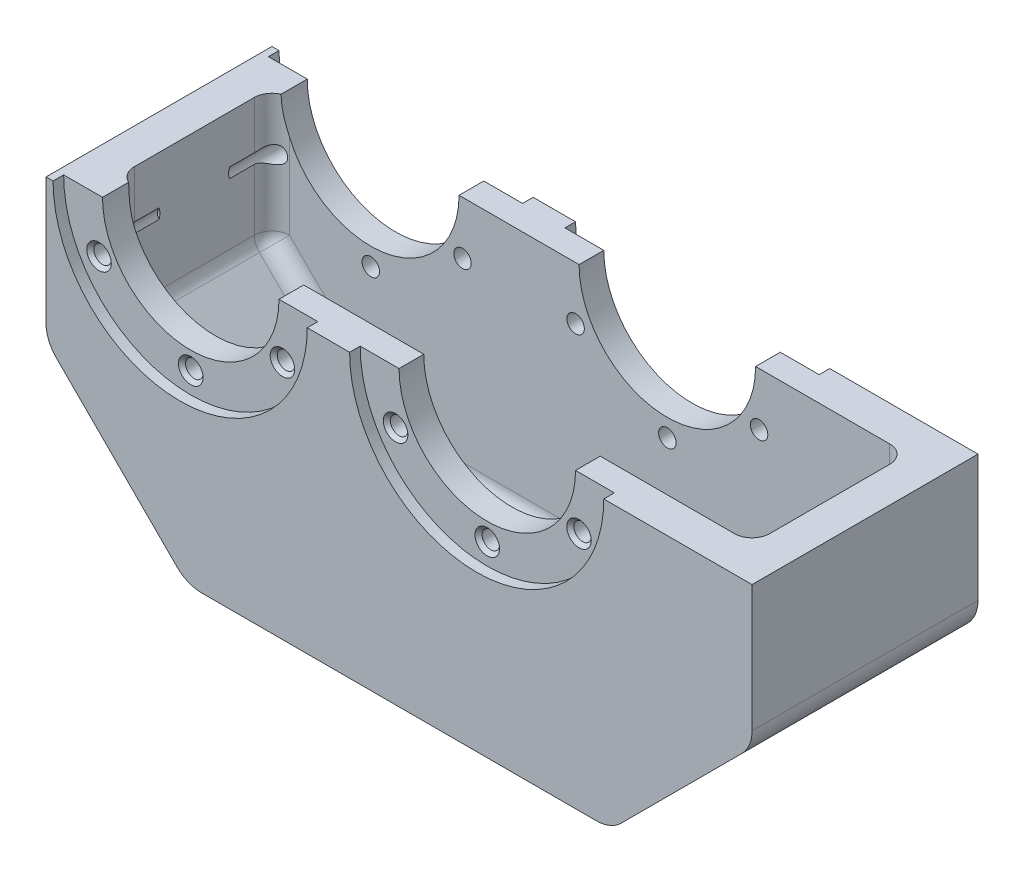
SolidWorks part; units mm, degrees
material "Сталь 20 ГОСТ 1050-88"
ref_plane "Plane1" through (0, 0, 0) normal (0, 0, 1) x (1, 0, 0)
ref_plane "Plane2" through (0, 0, 0) normal (0, 1, 0) x (1, 0, 0)
ref_plane "Plane3" through (0, 0, 0) normal (1, 0, 0) x (0, 0, -1)
sketch "Эскиз1" plane through (0, 0, 0) normal (0, 0, 1) x (1, 0, 0)
  line L0 (-38, 0) -> (-25, 0)
  line L1 (-38, 0) -> (-38, -40)
  line L2 (2, -80) -> (122, -80)
  line L3 (162, -40) -> (162, 0)
  line L4 (25, 0) -> (59, 0)
  line L5 (-38, -40) -> (2, -80)
  line L6 (162, -40) -> (122, -80)
  line L7 (109, 0) -> (162, 0)
  arc A0 (-25, 0) -> (25, 0) centre (0, 0) ccw
  arc A1 (59, 0) -> (109, 0) centre (84, 0) ccw
  dimension "D1" = 50
  dimension "D8" = 84
  dimension "D2" = 38
  dimension "D3" = 80
  dimension "D4" = 200
  dimension "D5" = 45
  dimension "D6" = 45
  dimension "D7" = 40
extrude "Бобышка-Вытянуть1" add sketch "Эскиз1" along normal mid plane 64
shell "Оболочка1" thickness 10
sketch "Эскиз2" plane through (0, 0, 32) normal (0, 0, 1) x (1, 0, 0)
  circle A0 centre (0, 0) radius 36
  circle A1 centre (84, 0) radius 36
  dimension "D1" = 72
extrude "Вырез-Вытянуть1" cut sketch "Эскиз2" against normal blind 3
sketch "Эскиз3" plane through (0, 0, -32) normal (0, 0, -1) x (-1, 0, 0)
  circle A0 centre (0, 0) radius 36
  arc A1 (-36, 0) -> (36, 0) centre (0, 0) ccw construction
  circle A2 centre (-84, 0) radius 36
extrude "Вырез-Вытянуть2" cut sketch "Эскиз3" against normal blind 3
fillet "Скругление1" radius 5 14 edges at (152, -35.8579, 0) (134.9289, -52.9289, 22) (134.9289, -52.9289, -22) (-10.9289, -52.9289, 22) (-28, -35.8579, 0) (-10.9289, -52.9289, -22) (117.8579, -70, 0) (62, -70, 22) (6.1421, -70, 0) (62, -70, -22) (-28, -17.9289, 22) (-28, -17.9289, -22) (152, -17.9289, 22) (152, -17.9289, -22)
fillet "Скругление2" radius 10 4 edges at (162, -40, 0) (122, -80, 0) (2, -80, 0) (-38, -40, 0)
hole_wizard "Отверстие обработанное метчиком M61" positions "Эскиз7" profile "Эскиз6" tap size "M6" standard "ISO"
sketch "Эскиз7" plane through (0, 0, 29) normal (0, 0, 1) x (1, 0, 0)
  point P0 (0, -30)
  dimension "D1" = 30
sketch "Эскиз6" plane through (0, -30, 29) normal (1, 0, 0) x (0, -1, 0)
  line L0 (0, 0) -> (0, 20.4871)
  line L1 (0, 20.4871) -> (2.475, 19)
  line L2 (2.475, 19) -> (2.475, 1)
  line L3 (2.475, 1) -> (3.475, 0)
  line L5 (3.475, 0) -> (0, 0)
  line L6 (-2.475, 1) -> (-3.475, 0) construction
  line L10 (0, 20.4871) -> (-2.475, 19) construction
  line L11 (0, -6.35) -> (0, 107.95) construction
  dimension "Диаметр сверла" = 4.95
  dimension "Глубина сверла" = 19
  dimension "Диаметр передней зенковки" = 6.95
  dimension "Угол передней зенковки" = 90
  dimension "Угол заточки сверла" = 118
cosmetic thread "Отверстие резьбы1" parameters "D1"=7, "D2"=6
hole_wizard "Отверстие обработанное метчиком M62" positions "Эскиз9" profile "Эскиз8" tap size "M6" standard "ISO"
sketch "Эскиз9" plane through (0, 0, -29) normal (0, 0, -1) x (-1, 0, 0)
  point P0 (0, -30)
sketch "Эскиз8" plane through (0, -30, -29) normal (1, 0, 0) x (0, 1, 0)
  line L0 (0, 0) -> (0, 20.4871)
  line L1 (0, 20.4871) -> (2.475, 19)
  line L2 (2.475, 19) -> (2.475, 1)
  line L3 (2.475, 1) -> (3.475, 0)
  line L5 (3.475, 0) -> (0, 0)
  line L6 (-2.475, 1) -> (-3.475, 0) construction
  line L10 (0, 20.4871) -> (-2.475, 19) construction
  line L11 (0, -6.35) -> (0, 107.95) construction
  dimension "Диаметр сверла" = 4.95
  dimension "Глубина сверла" = 19
  dimension "Диаметр передней зенковки" = 6.95
  dimension "Угол передней зенковки" = 90
  dimension "Угол заточки сверла" = 118
cosmetic thread "Отверстие резьбы2" parameters "D1"=7, "D2"=6
pattern_circular "Круговой массив1" count 6 over 360 about axis through (0, 0, 0) along (0, 0, 1) skipping 2, 3, 4 of "Отверстие обработанное метчиком M61", "Отверстие обработанное метчиком M62"
hole_wizard "Отверстие обработанное метчиком M63" positions "Эскиз11" profile "Эскиз10" tap size "M6" standard "ISO"
sketch "Эскиз11" plane through (0, 0, 29) normal (0, 0, 1) x (1, 0, 0)
  point P0 (84, -30)
  dimension "D1" = 30
sketch "Эскиз10" plane through (84, -30, 29) normal (1, 0, 0) x (0, -1, 0)
  line L0 (0, 0) -> (0, 20.4871)
  line L1 (0, 20.4871) -> (2.475, 19)
  line L2 (2.475, 19) -> (2.475, 1)
  line L3 (2.475, 1) -> (3.475, 0)
  line L5 (3.475, 0) -> (0, 0)
  line L6 (-2.475, 1) -> (-3.475, 0) construction
  line L10 (0, 20.4871) -> (-2.475, 19) construction
  line L11 (0, -6.35) -> (0, 107.95) construction
  dimension "Диаметр сверла" = 4.95
  dimension "Глубина сверла" = 19
  dimension "Диаметр передней зенковки" = 6.95
  dimension "Угол передней зенковки" = 90
  dimension "Угол заточки сверла" = 118
cosmetic thread "Отверстие резьбы3" parameters "D1"=7, "D2"=6
hole_wizard "Отверстие обработанное метчиком M64" positions "Эскиз13" profile "Эскиз12" tap size "M6" standard "ISO"
sketch "Эскиз13" plane through (0, 0, -29) normal (0, 0, -1) x (-1, 0, 0)
  point P0 (-84, -30)
sketch "Эскиз12" plane through (84, -30, -29) normal (1, 0, 0) x (0, 1, 0)
  line L0 (0, 0) -> (0, 20.4871)
  line L1 (0, 20.4871) -> (2.475, 19)
  line L2 (2.475, 19) -> (2.475, 1)
  line L3 (2.475, 1) -> (3.475, 0)
  line L5 (3.475, 0) -> (0, 0)
  line L6 (-2.475, 1) -> (-3.475, 0) construction
  line L10 (0, 20.4871) -> (-2.475, 19) construction
  line L11 (0, -6.35) -> (0, 107.95) construction
  dimension "Диаметр сверла" = 4.95
  dimension "Глубина сверла" = 19
  dimension "Диаметр передней зенковки" = 6.95
  dimension "Угол передней зенковки" = 90
  dimension "Угол заточки сверла" = 118
cosmetic thread "Отверстие резьбы4" parameters "D1"=7, "D2"=6
pattern_circular "Круговой массив2" count 6 over 360 about axis through (84, 0, 0) along (0, 0, 1) skipping 2, 3, 4 of "Отверстие обработанное метчиком M63", "Отверстие обработанное метчиком M64"
